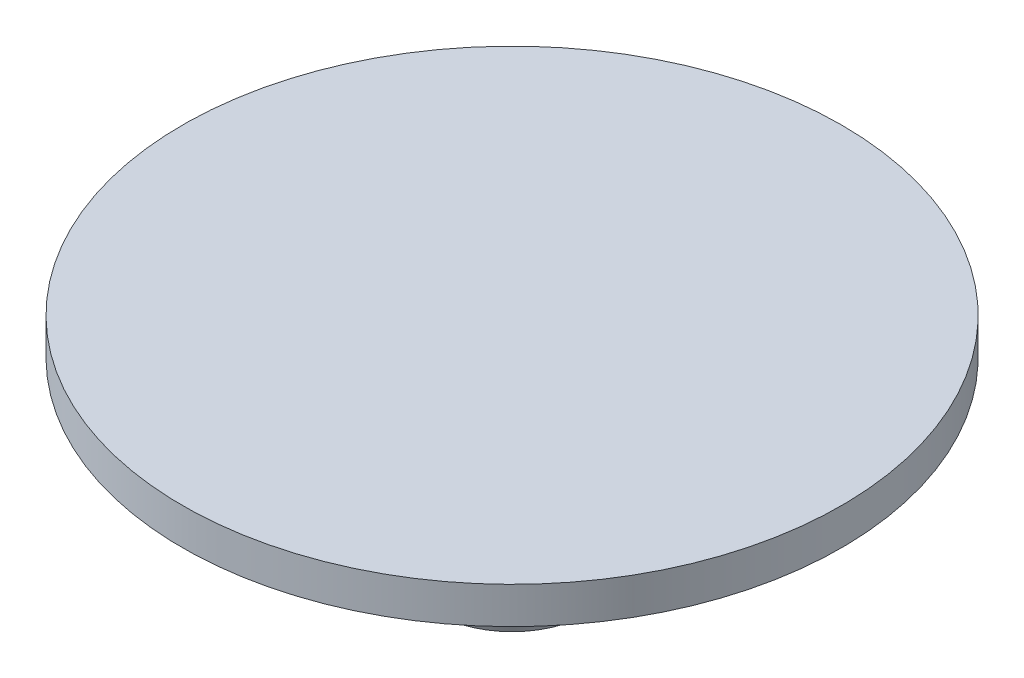
SolidWorks part; units mm, degrees
ref_plane "Front Plane" through (0, 0, 0) normal (0, 0, 1) x (1, 0, 0)
ref_plane "Top Plane" through (0, 0, 0) normal (0, 1, 0) x (1, 0, 0)
ref_plane "Right Plane" through (0, 0, 0) normal (1, 0, 0) x (0, 0, -1)
sketch "Sketch1" plane through (0, 0, 0) normal (0, 0, 1) x (1, 0, 0)
  line L1 (0, 0) -> (0, 6)
  line L2 (-3, 3) -> (-2.1, 3)
  line L3 (-2.1, 3) -> (-2.1, 5)
  line L4 (-2.1, 5) -> (-9, 5)
  line L7 (0, 6) -> (0, 0) construction
  line L8 (-3, 3) -> (-2.1, 0)
  line L9 (-2.1, 0) -> (0, 0)
  line L11 (0, 0) -> (0, 6) construction
  line L12 (-9, 5) -> (-9, 6)
  line L13 (-9, 6) -> (0, 6)
  point P2 (0, 0)
  point P3 (0, 0)
  dimension "D1" = 2
  dimension "D2" = 0
  dimension "D3" = 2.1
  dimension "D4" = 3
  dimension "D5" = 1
  dimension "D6" = 3
  dimension "D7" = 2.1
  dimension "D8" = 9
revolve "Revolve1" add sketch "Sketch1" angle 360 about L1
